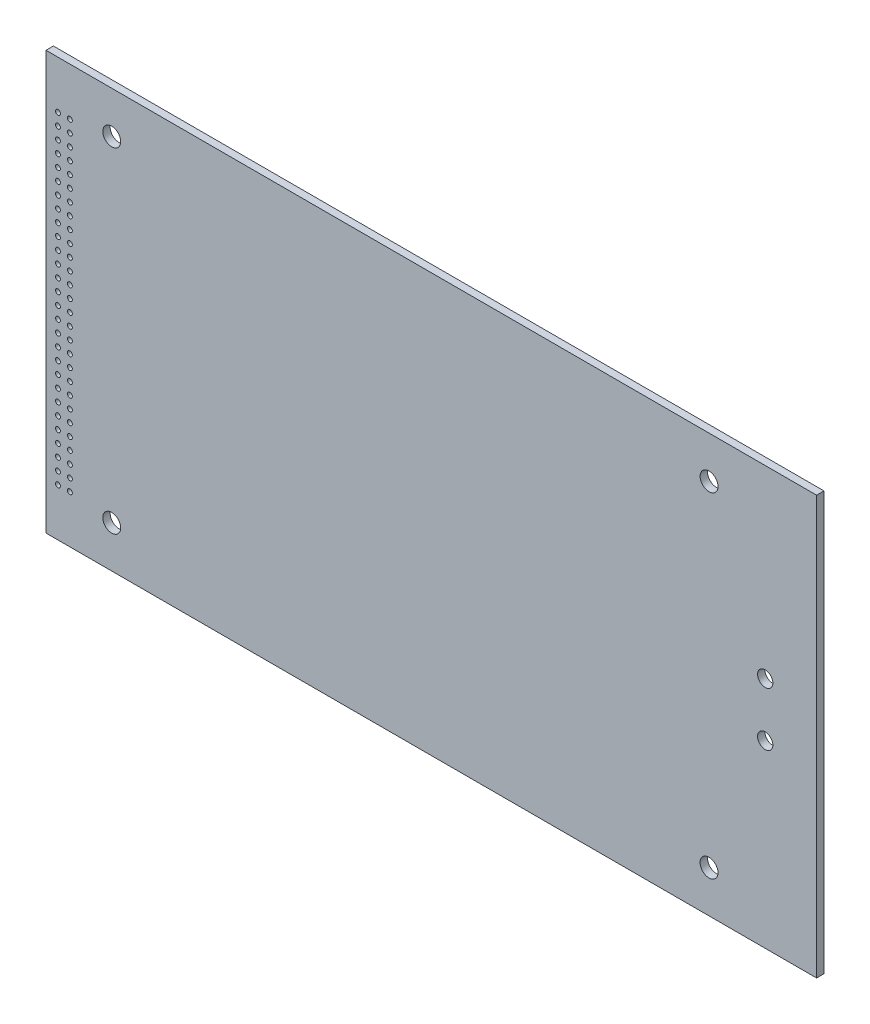
SolidWorks part; units mm, degrees
ref_plane "Front" through (0, 0, 0) normal (0, 0, 1) x (1, 0, 0)
ref_plane "Top" through (0, 0, 0) normal (0, 1, 0) x (1, 0, 0)
ref_plane "Right" through (0, 0, 0) normal (1, 0, 0) x (0, 0, -1)
sketch "Sketch1" plane through (0, 0, 0) normal (0, 0, 1) x (1, 0, 0)
  line L1 (0, 0) -> (163.83, 0)
  line L2 (0, 0) -> (0, -88.9)
  line L3 (0, -88.9) -> (163.83, -88.9)
  line L4 (163.83, 0) -> (163.83, -88.9)
  dimension "D1" = 163.83
  dimension "D2" = 88.9
extrude "Extrude1" add sketch "Sketch1" along normal blind 1.5748
sketch "Sketch3" plane through (0, 0, 1.5748) normal (0, 0, 1) x (1, 0, 0)
  line L0 (0, -88.9) -> (163.83, -88.9) construction
  line L1 (163.83, -88.9) -> (163.83, 0) construction
  circle A0 centre (152.908, -50.673) radius 1.6256
  circle A1 centre (152.908, -39.243) radius 1.6256
  dimension "D1" = 3.2512
  dimension "D4" = 3.2512
  dimension "D2" = 38.227
  dimension "D3" = 10.922
  dimension "D5" = 11.43
extrude "Cut-Extrude2" cut sketch "Sketch3" against normal blind 10
sketch "Sketch4" plane through (0, 0, 1.5748) normal (0, 0, 1) x (1, 0, 0)
  line L0 (0, -88.9) -> (163.83, -88.9) construction
  line L1 (0, 0) -> (0, -88.9) construction
  circle A0 centre (13.97, -80.01) radius 1.905
  dimension "D1" = 3.81
  dimension "D2" = 8.89
  dimension "D3" = 13.97
extrude "Mount Holes" cut sketch "Sketch4" against normal blind 10
pattern_linear "Mount Hole Pattern" count 2 spacing 71.12 along (0, 1, 0) count 2 spacing 127 along (1, 0, 0) of "Mount Holes"
sketch "Mount pin holes" plane through (0, 0, 1.5748) normal (0, 0, 1) x (1, 0, 0)
  line L0 (0, -88.9) -> (163.83, -88.9) construction
  line L1 (0, 0) -> (0, -88.9) construction
  circle A0 centre (2.54, -78.74) radius 0.52
  dimension "D1" = 1.04
  dimension "D2" = 10.16
  dimension "D3" = 2.54
extrude "Connector Pin 1" cut sketch "Mount pin holes" against normal blind 2.54
pattern_linear "LPattern1" count 28 spacing 2.54 along (0, 1, 0) count 2 spacing 2.54 along (1, 0, 0) of "Connector Pin 1"
